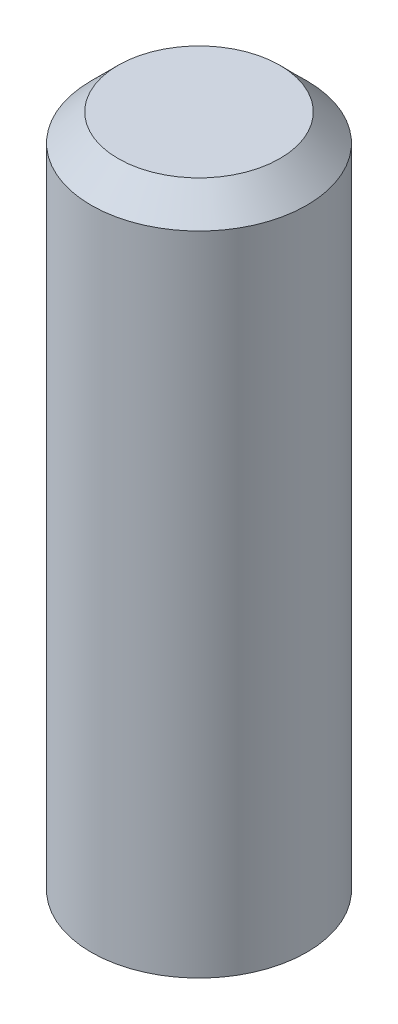
SolidWorks part; units mm, degrees
ref_plane "Front" through (0, 0, 0) normal (0, 0, 1) x (1, 0, 0)
ref_plane "Top" through (0, 0, 0) normal (0, 1, 0) x (1, 0, 0)
ref_plane "Right" through (0, 0, 0) normal (1, 0, 0) x (0, 0, -1)
sketch "Sketch1" plane through (0, 0, 0) normal (0, 1, 0) x (1, 0, 0)
  circle A0 centre (0, 0) radius 4
  dimension "D1" = 8
extrude "Boss-Extrude1" add sketch "Sketch1" along normal blind 25
chamfer "Chamfer1" distance 1 angle 45 1 edges at (0, 25, 4)
hole_wizard "M5 Tapped Hole1" positions "Sketch3" profile "Sketch2" tap size "M5" standard "ISO"
sketch "Sketch3" plane through (0, 0, 0) normal (0, -1, 0) x (1, 0, 0)
  point P0 (0, 0)
sketch "Sketch2" plane through (0, 0, 0) normal (1, 0, 0) x (0, 0, -1)
  line L0 (0, 0) -> (0, 7.2618)
  line L1 (0, 7.2618) -> (2.1, 6)
  line L2 (2.1, 6) -> (2.1, 0)
  line L5 (2.1, 0) -> (0, 0)
  line L10 (0, 7.2618) -> (-2.1, 6) construction
  line L11 (0, -6.35) -> (0, 107.95) construction
  dimension "Tap Drill Dia." = 4.2
  dimension "Tap Drill Depth" = 6
  dimension "Drill Angle" = 118
cosmetic thread "Hole Thread1" parameters "D1"=5, "D2"=5
